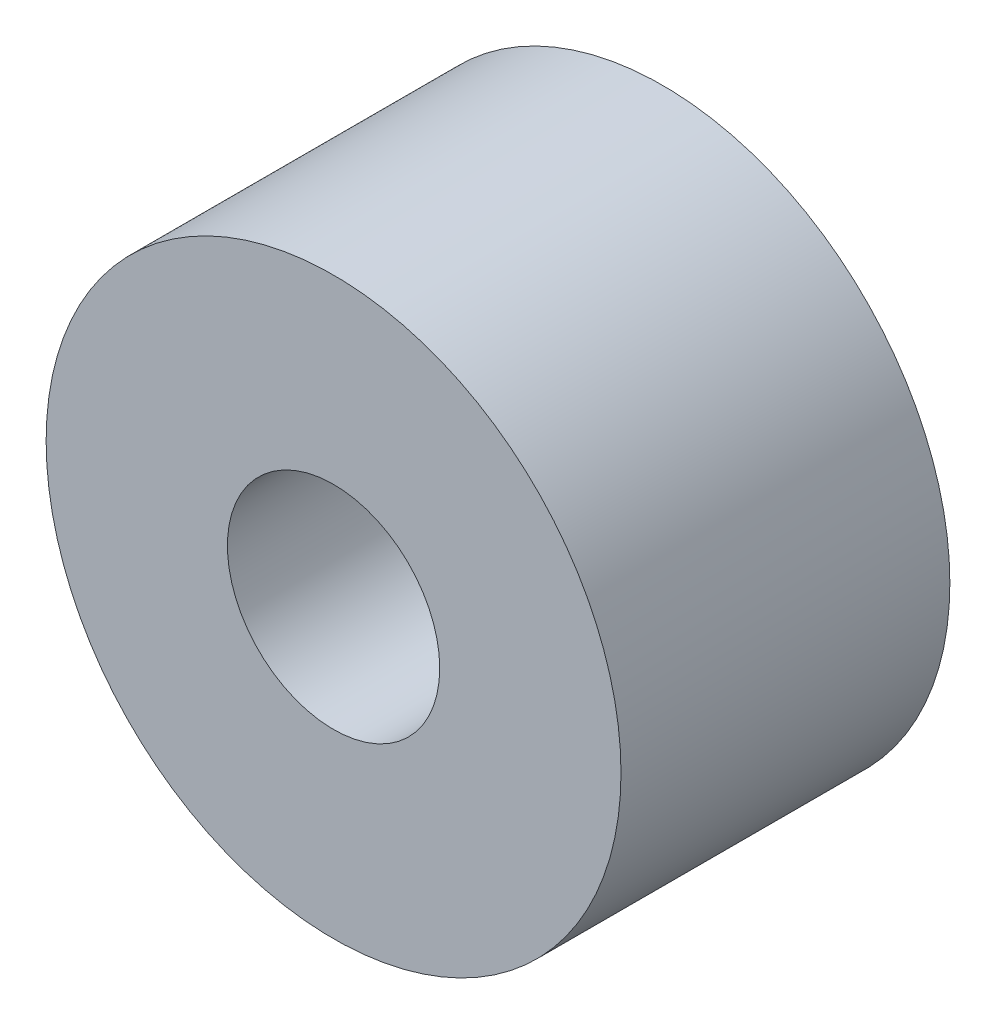
SolidWorks part; units mm, degrees
ref_plane "Front Plane" through (0, 0, 0) normal (0, 0, 1) x (1, 0, 0)
ref_plane "Top Plane" through (0, 0, 0) normal (0, 1, 0) x (1, 0, 0)
ref_plane "Right Plane" through (0, 0, 0) normal (1, 0, 0) x (0, 0, -1)
sketch "Sketch1" plane through (0, 0, 0) normal (0, 0, 1) x (1, 0, 0)
  circle A0 centre (0, 0) radius 2.05
  circle A1 centre (0, 0) radius 5.55
  dimension "D1" = 4.1
  dimension "D2" = 3.5
extrude "Boss-Extrude1" add sketch "Sketch1" along normal blind 6.35
